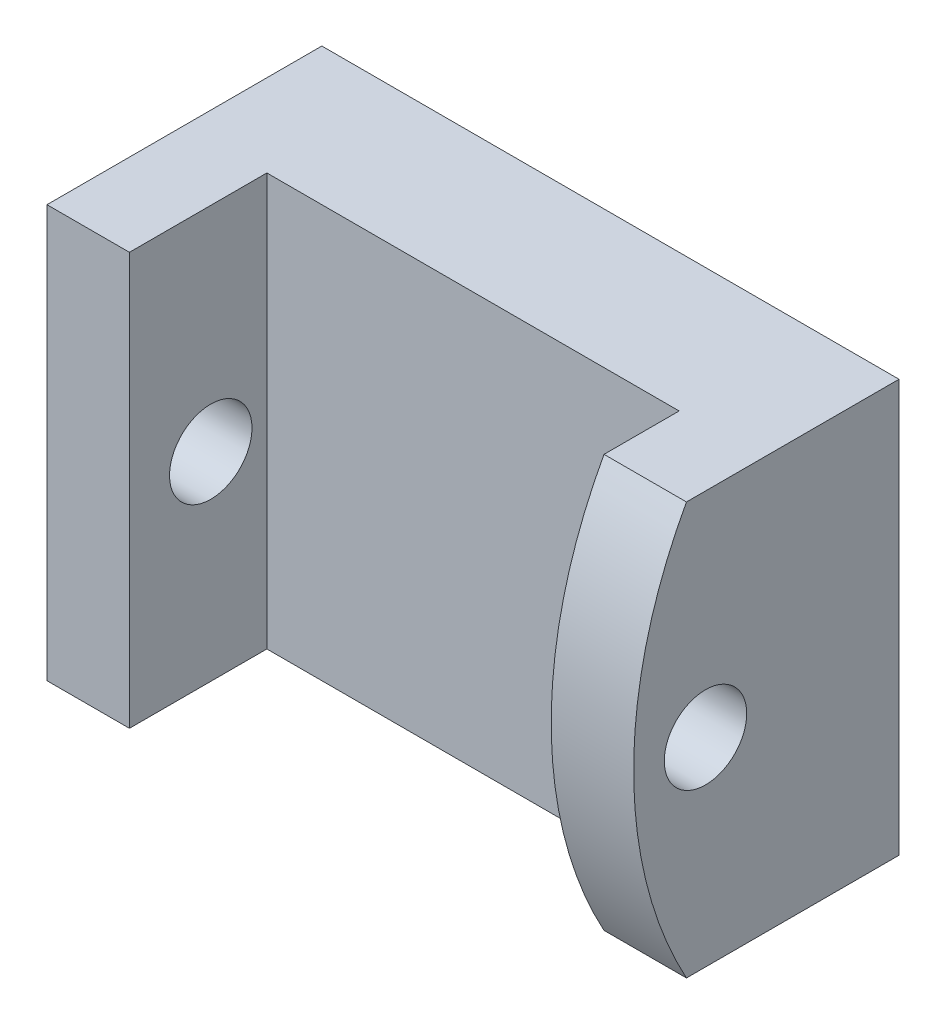
SolidWorks part; units mm, degrees
ref_plane "Front Plane" through (0, 0, 0) normal (0, 0, 1) x (1, 0, 0)
ref_plane "Top Plane" through (0, 0, 0) normal (0, 1, 0) x (1, 0, 0)
ref_plane "Right Plane" through (0, 0, 0) normal (1, 0, 0) x (0, 0, -1)
sketch "Sketch1" plane through (0, 0, 0) normal (0, 0, 1) x (1, 0, 0)
  line L1 (0, 0) -> (-21, 0)
  line L2 (0, 0) -> (0, -15)
  line L3 (0, -15) -> (-21, -15)
  line L4 (-21, 0) -> (-21, -15)
  dimension "D1" = 15
  dimension "D2" = 21
extrude "Boss-Extrude1" add sketch "Sketch1" along normal blind 5
sketch "Sketch2" plane through (0, 0, 5) normal (0, 0, 1) x (1, 0, 0)
  line L0 (0, 0) -> (-21, 0) construction
  line L1 (-3, 0) -> (0, 0)
  line L2 (-3, 0) -> (-3, -15)
  line L3 (-3, -15) -> (0, -15)
  line L4 (0, 0) -> (0, -15)
  line L5 (-21, -15) -> (0, -15) construction
  line L6 (0, -15) -> (0, 0) construction
  line L7 (-10.5, 0) -> (-10.5, -15) construction
  line L8 (-21, 0) -> (-18, 0)
  line L9 (-21, 0) -> (-21, -15)
  line L10 (-21, -15) -> (-18, -15)
  line L11 (-18, 0) -> (-18, -15)
  dimension "D1" = 3
  dimension "D2" = 3
extrude "Boss-Extrude2" add sketch "Sketch2" along normal blind 5
sketch "Sketch3" plane through (0, 0, 0) normal (1, 0, 0) x (0, 0, -1)
  line L0 (-10, 0) -> (-7.4945, 0)
  line L2 (-10, 0) -> (-10, -15)
  line L3 (-10, 0) -> (0, 0) construction
  line L4 (-7.4945, 0) -> (-7.4945, -15)
  line L5 (-10, -15) -> (0, -15) construction
  line L6 (-7.4945, -15) -> (-10, -15)
  arc A0 (-7.7337, 0) -> (-7.7337, -15) centre (5.9451, -7.5) ccw
  line M8 (-10, 0) -> (-10, -15)
  line M9 (-10, -15) -> (0, -15)
extrude "Cut-Extrude1" cut sketch "Sketch3" against normal blind 18 contours A0 L0 M8 M9
sketch "Sketch4" plane through (-18, 0, 0) normal (1, 0, 0) x (0, 0, -1)
  circle A0 centre (-7.0414, -7.7625) radius 1.5
  dimension "D1" = 3
extrude "Cut-Extrude2" cut sketch "Sketch4" against normal through all both and the other way through all
